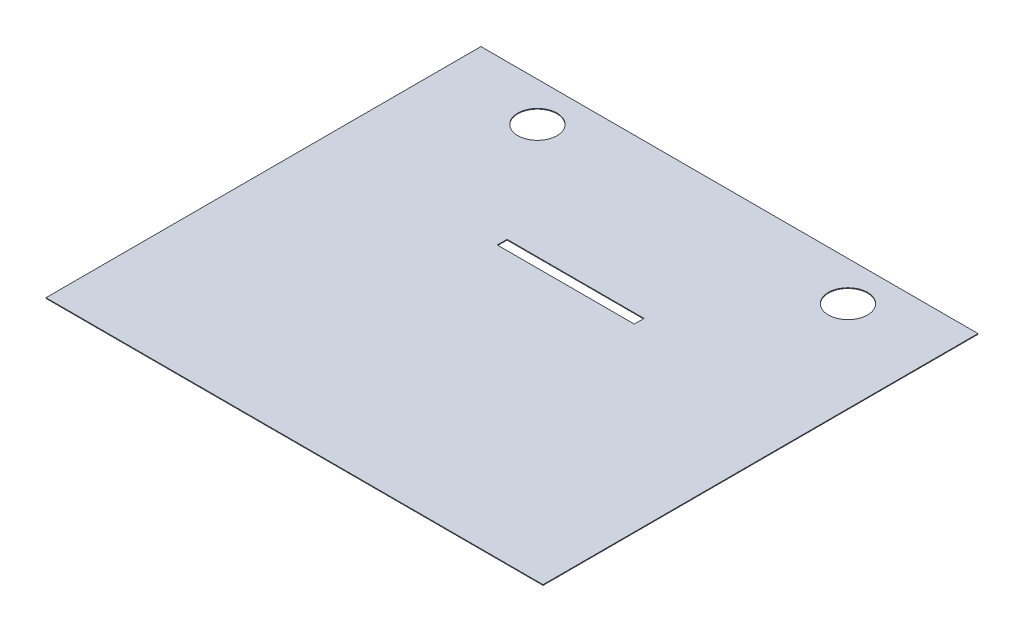
SolidWorks part; units mm, degrees
material "A-Glass Fiber"
ref_plane "Front Plane" through (0, 0, 0) normal (0, 0, 1) x (1, 0, 0)
ref_plane "Top Plane" through (0, 0, 0) normal (0, 1, 0) x (1, 0, 0)
ref_plane "Right Plane" through (0, 0, 0) normal (1, 0, 0) x (0, 0, -1)
sketch "Sketch1" plane through (0, 0, 0) normal (0, 1, 0) x (1, 0, 0)
  line L0 (25.9, 29.225) -> (32.9, 29.225)
  line L1 (0, 0) -> (50.8, 0)
  line L2 (0, 0) -> (0, 44.45)
  line L3 (0, 44.45) -> (50.8, 44.45)
  line L4 (50.8, 0) -> (50.8, 44.45)
  line L5 (20.4, 27.225) -> (30.4, 27.225)
  line L6 (20.4, 27.225) -> (20.4, 17.225)
  line L7 (20.4, 17.225) -> (30.4, 17.225)
  line L8 (30.4, 27.225) -> (30.4, 17.225)
  line L9 (17.9, 15.225) -> (32.9, 15.225)
  line L10 (17.9, 15.225) -> (17.9, 29.225)
  line L11 (17.9, 29.225) -> (24.9, 29.225)
  line L12 (32.9, 15.225) -> (32.9, 29.225)
  line L14 (22.9, 44.45) -> (22.9, 39.45)
  line L15 (22.9, 39.45) -> (24.9, 39.45)
  line L16 (27.9, 44.45) -> (27.9, 39.45)
  line L18 (24.9, 39.45) -> (24.9, 29.225)
  line L20 (25.9, 39.45) -> (25.9, 29.225)
  line L21 (25.9, 39.45) -> (27.9, 39.45)
  line L22 (5, 38.4487) -> (0, 38.4487)
  line L31 (5, 25.4487) -> (5, 23.4487)
  line L32 (45.8, 35.4487) -> (45.8, 33.4487)
  line L49 (18.4, 27.725) -> (32.4, 27.725)
  line L50 (18.4, 27.725) -> (18.4, 28.725)
  line L51 (18.4, 28.725) -> (32.4, 28.725)
  line L52 (32.4, 27.725) -> (32.4, 28.725)
  line L53 (50.8, 38.4487) -> (45.8, 38.4487)
  line L55 (50.8, 33.4487) -> (45.8, 33.4487)
  line L56 (45.8, 38.4487) -> (45.8, 36.4487)
  line L57 (45.8, 36.4487) -> (33.9, 36.4487)
  line L59 (45.8, 35.4487) -> (34.9, 35.4487)
  line L62 (33.9, 36.4487) -> (33.9, 15.225)
  line L63 (33.9, 15.225) -> (34.9, 15.225)
  line L64 (34.9, 35.4487) -> (34.9, 15.225)
  line L65 (45.8, 15.225) -> (45.8, 13.225)
  line L67 (35.9, 15.225) -> (35.9, 29.225)
  line L68 (35.9, 29.225) -> (36.9, 29.225)
  line L69 (36.9, 16.225) -> (36.9, 29.225)
  line L70 (35.9, 15.225) -> (45.8, 15.225)
  line L72 (36.9, 16.225) -> (45.8, 16.225)
  line L74 (50.8, 18.225) -> (45.8, 18.225)
  line L76 (50.8, 13.225) -> (45.8, 13.225)
  line L77 (45.8, 18.225) -> (45.8, 16.225)
  line L78 (5, 35.4487) -> (5, 33.4487)
  line L81 (0, 33.4487) -> (5, 33.4487)
  line L82 (5, 38.4487) -> (5, 36.4487)
  line L83 (5, 36.4487) -> (16.9, 36.4487)
  line L85 (5, 35.4487) -> (15.9, 35.4487)
  line L88 (16.9, 36.4487) -> (16.9, 15.225)
  line L89 (16.9, 15.225) -> (15.9, 15.225)
  line L90 (15.9, 35.4487) -> (15.9, 15.225)
  line L91 (0, 28.4487) -> (5, 28.4487)
  line L93 (0, 23.4487) -> (5, 23.4487)
  line L94 (5, 28.4487) -> (5, 26.4487)
  line L103 (5, 26.4487) -> (13.9, 26.4487)
  line L105 (5, 25.4487) -> (13.9, 25.4487)
  line L107 (14.9, 29.225) -> (13.9, 29.225)
  line L108 (14.9, 29.225) -> (14.9, 23.4487)
  line L109 (14.9, 23.4487) -> (13.9, 23.4487)
  line L110 (13.9, 29.225) -> (13.9, 26.4487)
  line L111 (13.9, 22.9487) -> (14.9, 22.9487)
  line L112 (13.9, 22.9487) -> (13.9, 16.225)
  line L114 (14.9, 22.9487) -> (14.9, 15.225)
  line L119 (14.9, 15.225) -> (5, 15.225)
  line L121 (13.9, 16.225) -> (5, 16.225)
  line L123 (0, 18.225) -> (5, 18.225)
  line L125 (0, 13.225) -> (5, 13.225)
  line L126 (5, 18.225) -> (5, 16.225)
  line L127 (13.9, 25.4487) -> (13.9, 23.4487)
  line L128 (5, 15.225) -> (5, 13.225)
  line L130 (18.9, 5) -> (20.9, 5)
  line L131 (17.9, 14.725) -> (32.9, 14.725)
  line L133 (18.9, 13.725) -> (32.9, 13.725)
  line L134 (32.9, 14.725) -> (32.9, 13.725)
  line L136 (17.9, 14.725) -> (17.9, 5)
  line L138 (18.9, 13.725) -> (18.9, 5)
  line L140 (15.9, 0) -> (15.9, 5)
  line L141 (15.9, 5) -> (17.9, 5)
  line L142 (20.9, 0) -> (20.9, 5)
  line L143 (19.4, 13.225) -> (32.9, 13.225)
  line L144 (19.4, 13.225) -> (19.4, 12.225)
  line L145 (19.4, 12.225) -> (31.9, 12.225)
  line L148 (32.9, 13.225) -> (32.9, 5)
  line L150 (31.9, 12.225) -> (31.9, 5)
  line L152 (29.9, 0) -> (29.9, 5)
  line L153 (29.9, 5) -> (31.9, 5)
  line L154 (34.9, 0) -> (34.9, 5)
  line L155 (32.9, 5) -> (34.9, 5)
  circle A0 centre (9.7727, 40.45) radius 2.0013
  circle A1 centre (41.5129, 40.45) radius 2
  point P13 (32.9, 22.225)
  point P22 (27.9, 41.95)
  point P77 (14.4, 23.4487)
  dimension "D17" = 4
  dimension "D19" = 4
  dimension "D20" = 4.0026
  dimension "D1" = 50.8
  dimension "D2" = 44.45
  dimension "D3" = 10
  dimension "D4" = 10
  dimension "D5" = 20.4
  dimension "D6" = 17.225
  dimension "D7" = 2.5
  dimension "D8" = 2.5
  dimension "D9" = 2
  dimension "D10" = 2
  dimension "D11" = 5
  dimension "D12" = 5
  dimension "D13" = 2
  dimension "D14" = 22.9
  dimension "D15" = 2
  dimension "D16" = 14
  dimension "D18" = 4
  dimension "D21" = 0.5
  dimension "D22" = 1
  dimension "D23" = 5
  dimension "D24" = 5
  dimension "D25" = 5
  dimension "D26" = 5
  dimension "D27" = 2
  dimension "D28" = 1
  dimension "D29" = 1
  dimension "D30" = 1
  dimension "D31" = 1
  dimension "D32" = 2
  dimension "D33" = 2
  dimension "D34" = 5
  dimension "D35" = 5
  dimension "D36" = 5
  dimension "D37" = 5
  dimension "D38" = 2
  dimension "D39" = 2
  dimension "D40" = 1
  dimension "D41" = 1
  dimension "D42" = 2
  dimension "D43" = 1
  dimension "D44" = 1
  dimension "D45" = 0.5
  dimension "D46" = 10.225
  dimension "D47" = 0.5
  dimension "D48" = 2
  dimension "D49" = 2
  dimension "D50" = 2
  dimension "D51" = 0
  dimension "D52" = 1
  dimension "D53" = 1
  dimension "D54" = 0.5
  dimension "D55" = 1
  dimension "D56" = 2
  dimension "D57" = 5
  dimension "D58" = 2
  dimension "D59" = 2
  dimension "D60" = 1
  dimension "D61" = 5
  dimension "D62" = 0.5
  dimension "D63" = 0.5
  dimension "D64" = 1
  dimension "D66" = 1
  dimension "D67" = 2
  dimension "D68" = 2
  dimension "D69" = 5
sketch "Sketch2" plane through (0, 0, 0) normal (0, 1, 0) x (1, 0, 0)
  line L1 (0, 44.45) -> (50.8, 44.45)
  line L2 (0, 44.45) -> (0, 0)
  line L3 (0, 0) -> (50.8, 0)
  line L4 (50.8, 44.45) -> (50.8, 0)
  line L5 (18.4, 28.725) -> (32.4, 28.725)
  line L6 (18.4, 28.725) -> (18.4, 27.725)
  line L7 (18.4, 27.725) -> (32.4, 27.725)
  line L8 (32.4, 28.725) -> (32.4, 27.725)
  circle A0 centre (9.7727, 40.45) radius 2.0013
  circle A1 centre (41.5129, 40.45) radius 2
extrude "Boss-Extrude3" add sketch "Sketch2" against normal blind 0.07
